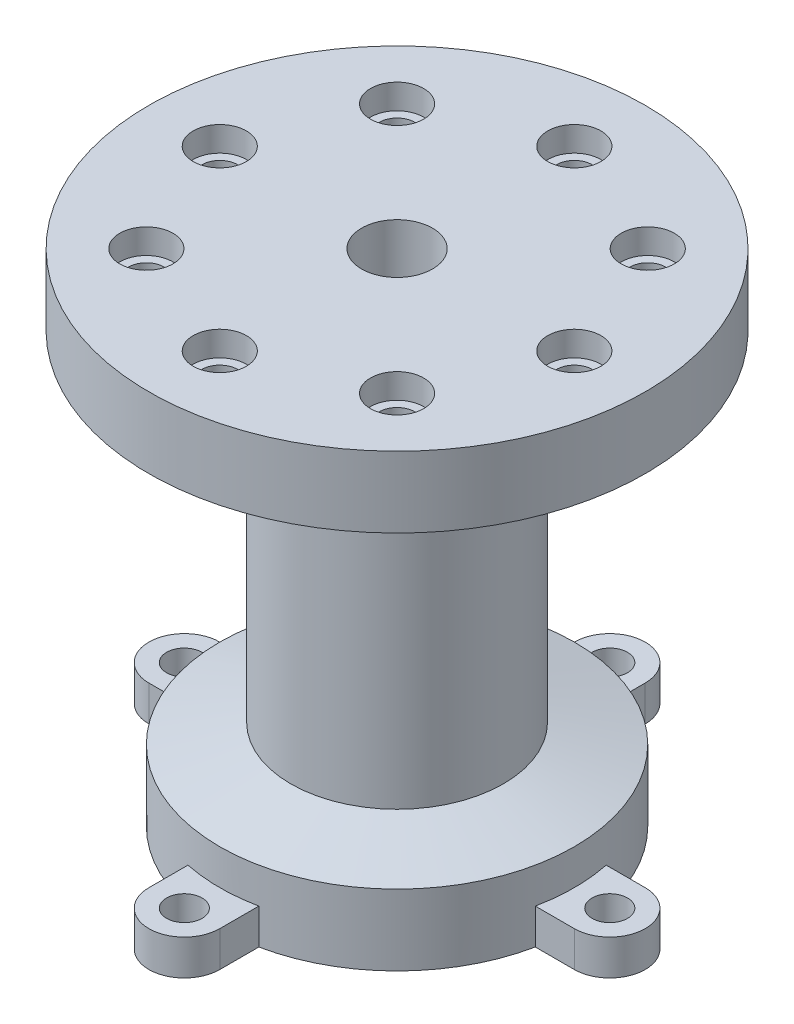
SolidWorks part; units mm, degrees
ref_plane "Front Plane" through (0, 0, 0) normal (0, 0, 1) x (1, 0, 0)
ref_plane "Top Plane" through (0, 0, 0) normal (0, 1, 0) x (1, 0, 0)
ref_plane "Right Plane" through (0, 0, 0) normal (1, 0, 0) x (0, 0, -1)
sketch "Sketch1" plane through (0, 0, 0) normal (0, 0, 1) x (1, 0, 0)
  line L0 (0, 0) -> (25, 0)
  line L1 (0, 70.5567) -> (0, 0)
  line L3 (25, 0) -> (25, 10)
  line L4 (25, 10) -> (15, 12.6795)
  line L5 (15, 12.6795) -> (15, 55.1977)
  line L6 (15, 55.1977) -> (35, 60.5567)
  line L7 (35, 60.5567) -> (35, 70.5567)
  line L8 (35, 70.5567) -> (0, 70.5567)
  line L9 (0, 0) -> (0, 18.488) construction
  dimension "D1" = 30
  dimension "D2" = 70
  dimension "D3" = 50
  dimension "D4" = 10
  dimension "D5" = 15
  dimension "D6" = 15
  dimension "D7" = 70.5567
  dimension "D8" = 10
revolve "Revolve1" add sketch "Sketch1" angle 360 about L9
sketch "Sketch2" plane through (0, 0, 0) normal (0, 1, 0) x (1, 0, 0)
  line L0 (0, 0) -> (0, -32.8762) construction
  line L1 (-5, -30) -> (-5, -24.4949)
  line L2 (5, -30) -> (5, -24.4949)
  circle A0 centre (0, 0) radius 25 construction
  arc A1 (-5, -24.4949) -> (5, -24.4949) centre (0, 0) ccw
  arc A2 (-5, -30) -> (5, -30) centre (0, -30) ccw
  circle A3 centre (0, -30) radius 2.5
  point P6 (0, -25)
  dimension "D2" = 10
  dimension "D3" = 5
  dimension "D1" = 5
extrude "Boss-Extrude1" add sketch "Sketch2" along normal blind 5
pattern_circular "CirPattern1" count 4 every 90 about axis through (0, 0, 0) along (0, 1, 0) of "Boss-Extrude1"
hole_wizard "Hole2" positions "Sketch5" profile "Sketch4" legacy
sketch "Sketch5" plane through (0, 70.5567, 0) normal (0, 1, 0) x (1, 0, 0)
  line L0 (0, 0) -> (0, 11.5702) construction
  line L2 (0, 0) -> (7.3738, 0) construction
  point P17 (0, 0)
sketch "Sketch4" plane through (0, 70.5567, 0) normal (1, 0, 0) x (0, 0, 1)
  line L0 (0, 0) -> (0, 24.5043)
  line L1 (0, 24.5043) -> (5, 21.5)
  line L2 (5, 21.5) -> (5, 0)
  line L4 (5, 0) -> (0, 0)
  line L6 (0, 24.5043) -> (-5, 21.5) construction
  line L7 (0, -4.2442) -> (0, 117.3081) construction
  dimension "Diameter" = 10
  dimension "Depth" = 21.5
  dimension "Drill Angle" = 118
hole_wizard "Hole9" positions "Sketch24" profile "Sketch25" legacy
sketch "Sketch24" plane through (0, 70.5567, 0) normal (0, 1, 0) x (1, 0, 0)
  line L0 (0, 0) -> (0, 16.7223) construction
  circle A0 centre (0, 0) radius 25
  point P11 (0, 25)
  point P17 (17.6777, 17.6777)
  point P18 (25, 0)
  point P19 (17.6777, -17.6777)
  point P20 (0, -25)
  point P21 (-17.6777, -17.6777)
  point P22 (-25, 0)
  point P23 (-17.6777, 17.6777)
  dimension "D1" = 50
  dimension "D2" = 8
sketch "Sketch25" plane through (-17.6777, 70.5567, -17.6777) normal (1, 0, 0) x (0, 0, 1)
  line L0 (0, 0) -> (0, 49.9844)
  line L1 (0, 49.9844) -> (2.5, 49.9844)
  line L2 (2.5, 49.9844) -> (2.5, 3.5)
  line L3 (2.5, 3.5) -> (3.75, 3.5)
  line L4 (3.75, 3.5) -> (3.75, 0)
  line L5 (3.75, 0) -> (0, 0)
  line L6 (0, 110) -> (0, -10) construction
  dimension "Diameter" = 5
  dimension "Depth" = 50
  dimension "C-Bore Diameter" = 7.5
  dimension "C-Bore Depth" = 3.5
